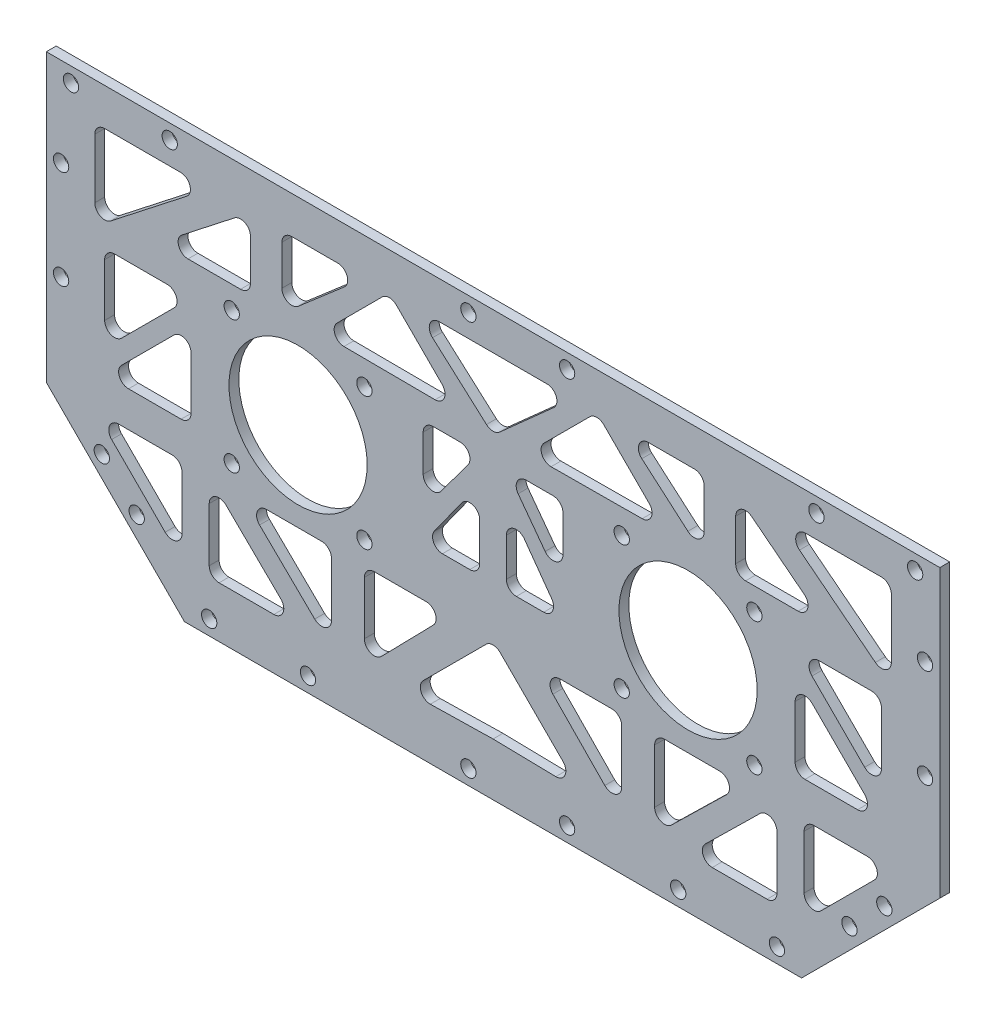
SolidWorks part; units mm, degrees
material "Thornel Mat VMA"
ref_plane "前视基准面" through (0, 0, 0) normal (0, 0, 1) x (1, 0, 0)
ref_plane "上视基准面" through (0, 0, 0) normal (0, 1, 0) x (1, 0, 0)
ref_plane "右视基准面" through (0, 0, 0) normal (1, 0, 0) x (0, 0, -1)
sketch "草图1" plane through (0, 0, 0) normal (0, 0, 1) x (1, 0, 0)
  line L0 (-39.5, 0) -> (39.5, 0) construction
  line L7 (-62.5, -32.4324) -> (70.1149, 36.3839) construction
  line L8 (-92.5, -48) -> (-80.6781, -41.8654) construction
  line L9 (-39.5, 0) -> (-52.935, -13.435) construction
  line L10 (-39.5, 0) -> (-39.5, -19) construction
  line L11 (-52.935, 13.435) -> (-26.065, -13.435) construction
  line L12 (-39.5, 0) -> (-26.065, 13.435) construction
  line L13 (26.065, 13.435) -> (39.5, 0) construction
  line L14 (39.5, 0) -> (52.935, -13.435) construction
  line L15 (39.5, 0) -> (39.5, -24.0416) construction
  line L16 (26.065, -13.435) -> (39.5, 0) construction
  line L17 (39.5, 0) -> (52.935, 13.435) construction
  line L18 (39.5, 0) -> (63.5416, 0) construction
  line L19 (-90.5, 18) -> (-90.5, -18)
  line L20 (-62.5, -46) -> (62.5, -46)
  line L21 (90.5, 18) -> (90.5, -18)
  line L23 (62.2753, 0) -> (62.2753, 18) construction
  line L25 (0, 48) -> (0, -63.7675) construction
  line L27 (-20, -40) -> (20, -40) construction
  line L28 (-20, -40) -> (-20, -46) construction
  line L29 (-20, -46) -> (20, -46) construction
  line L30 (20, -40) -> (20, -46) construction
  line L31 (-20, -40) -> (20, -46) construction
  line L32 (-20, -46) -> (20, -40) construction
  line L36 (-77.2639, -21.4142) -> (-66.4216, -32.2565)
  line L38 (-63.0074, -30.8423) -> (-63.0074, -20)
  line L51 (-62.5, 32.4324) -> (62.5, -32.4324) construction
  line L67 (0, 29.9183) -> (47.4731, 22.681) construction
  line L68 (48.1242, -22.4415) -> (0, -29.8407) construction
  line L93 (90.5, -18) -> (62.5, -46)
  line L94 (-62.5, -46) -> (-90.5, -18)
  line L95 (-90.5, 18) -> (-90.5, 39.9996)
  line L98 (90.5, 39.9996) -> (90.5, 18)
  line L99 (-65.0074, -18) -> (-75.8497, -18)
  line L100 (-57.5, -22.7661) -> (-57.5, -33.6707)
  line L101 (-55.5, -35.6707) -> (-44.3922, -35.6707)
  line L102 (-42.9911, -32.2435) -> (-54.0989, -21.3389)
  line L109 (-45.9021, -18) -> (-34.7336, -18)
  line L110 (-32.7336, -20) -> (-32.7336, -30.9185)
  line L112 (-36.1317, -32.3487) -> (-47.3002, -21.4301)
  line L114 (-26.065, -20) -> (-26.065, -30.764)
  line L115 (-22.6348, -32.1621) -> (-12.1117, -21.3981)
  line L116 (-13.5419, -18) -> (-24.065, -18)
  line L117 (-1.4142, -19.4142) -> (-14.1576, -32.1576)
  line L118 (-12.7034, -35.5714) -> (0, -35.3174)
  line L119 (-80.6781, 30.4324) -> (-80.6781, 18.4111)
  line L120 (-77.4461, 16.8356) -> (-62.0726, 28.8569)
  line L121 (-63.3045, 32.4324) -> (-78.6781, 32.4324)
  line L122 (-52.377, 29.9052) -> (-63.0295, 21.5755)
  line L123 (-61.7975, 18) -> (-51.145, 18)
  line L124 (-49.145, 20) -> (-49.145, 28.3297)
  line L125 (-1.3315, 19.1879) -> (-12.2625, 28.94)
  line L126 (-10.931, 32.4324) -> (10.931, 32.4324)
  line L127 (-42.7754, 30.4324) -> (-42.7754, 22.37)
  line L128 (-39.4682, 20.8564) -> (-30.1332, 28.9188)
  line L129 (-31.4405, 32.4324) -> (-40.7754, 32.4324)
  line L130 (-19.6046, 31.0182) -> (-10.3179, 21.7316)
  line L131 (-11.7442, 18.3174) -> (-30.206, 18.4289)
  line L132 (-31.6082, 21.8431) -> (-22.433, 31.0182)
  line L133 (1.3315, 19.1879) -> (12.2625, 28.94)
  line L134 (12.7034, -35.5714) -> (0, -35.3174)
  line L135 (1.4142, -19.4142) -> (14.1576, -32.1576)
  line L136 (63.0074, -30.8423) -> (63.0074, -20)
  line L137 (77.2639, -21.4142) -> (66.4216, -32.2565)
  line L138 (65.0074, -18) -> (75.8497, -18)
  line L139 (55.5, -35.6707) -> (44.3922, -35.6707)
  line L140 (57.5, -22.7661) -> (57.5, -33.6707)
  line L141 (42.9911, -32.2435) -> (54.0989, -21.3389)
  line L142 (32.7336, -20) -> (32.7336, -30.9185)
  line L143 (45.9021, -18) -> (34.7336, -18)
  line L144 (36.1317, -32.3487) -> (47.3002, -21.4301)
  line L145 (22.6348, -32.1621) -> (12.1117, -21.3981)
  line L146 (26.065, -20) -> (26.065, -30.764)
  line L147 (13.5419, -18) -> (24.065, -18)
  line L148 (77.4461, 16.8356) -> (62.0726, 28.8569)
  line L149 (80.6781, 30.4324) -> (80.6781, 18.4111)
  line L150 (63.3045, 32.4324) -> (78.6781, 32.4324)
  line L151 (61.7975, 18) -> (51.145, 18)
  line L152 (52.377, 29.9052) -> (63.0295, 21.5755)
  line L153 (49.145, 20) -> (49.145, 28.3297)
  line L154 (39.4682, 20.8564) -> (30.1332, 28.9188)
  line L155 (42.7754, 30.4324) -> (42.7754, 22.37)
  line L156 (31.4405, 32.4324) -> (40.7754, 32.4324)
  line L157 (11.7442, 18.3174) -> (30.206, 18.4289)
  line L158 (19.6046, 31.0182) -> (10.3179, 21.7316)
  line L159 (31.6082, 21.8431) -> (22.433, 31.0182)
  line L160 (-12.1576, 13.435) -> (-6.6802, 13.435)
  line L161 (-14.1576, 11.435) -> (-14.1576, 4.0523)
  line L162 (-10.5514, 2.8607) -> (-5.074, 10.2434)
  line L163 (-6.3308, 2.951) -> (-11.8845, -4.7851)
  line L164 (-10.2598, -7.9514) -> (-4.7061, -7.9514)
  line L165 (-2.7061, -5.9514) -> (-2.7061, 1.7846)
  line L175 (10.2598, -7.9514) -> (4.7061, -7.9514)
  line L176 (6.3308, 2.951) -> (11.8845, -4.7851)
  line L177 (2.7061, -5.9514) -> (2.7061, 1.7846)
  line L178 (14.1576, 11.435) -> (14.1576, 4.0523)
  line L179 (10.5514, 2.8607) -> (5.074, 10.2434)
  line L180 (12.1576, 13.435) -> (6.6802, 13.435)
  line L181 (-76.6781, 11.435) -> (-66.0151, 11.435)
  line L182 (-64.6009, 8.0208) -> (-75.2639, -2.6422)
  line L183 (-78.6781, -1.2279) -> (-78.6781, 9.435)
  line L184 (-64.6009, 3.2678) -> (-75.2639, -7.3952)
  line L185 (-73.8497, -10.8094) -> (-63.1867, -10.8094)
  line L186 (-61.1867, -8.8094) -> (-61.1867, 1.8536)
  line L187 (73.8497, -10.8094) -> (63.1867, -10.8094)
  line L188 (64.6009, 3.2678) -> (75.2639, -7.3952)
  line L189 (61.1867, -8.8094) -> (61.1867, 1.8536)
  line L190 (64.6009, 8.0208) -> (75.2639, -2.6422)
  line L191 (76.6781, 11.435) -> (66.0151, 11.435)
  line L192 (78.6781, -1.2279) -> (78.6781, 9.435)
  line L193 (62.5, -46) -> (62.5, -13.435) construction
  line L194 (-90.5, 39.9996) -> (90.5, 39.9996)
  line L195 (90.5, -18) -> (62.5, -18) construction
  line L196 (-90.5, -18) -> (-57.5, -18) construction
  line L197 (-62.5, -46) -> (-62.5, -18) construction
  circle A16 centre (-39.5, 0) radius 19 construction
  circle A30 centre (-52.935, -13.435) radius 1.55
  circle A33 centre (-52.935, 13.435) radius 1.55
  circle A34 centre (-26.065, -13.435) radius 1.55
  circle A35 centre (-26.065, 13.435) radius 1.55
  circle A48 centre (-39.5, 0) radius 14
  circle A49 centre (39.5, 0) radius 14
  circle A50 centre (57.5, -43) radius 1.55
  circle A51 centre (37.5, -43) radius 1.55
  circle A52 centre (-57.5, -43) radius 1.55
  circle A53 centre (-37.5, -43) radius 1.55
  circle A54 centre (-85.5, 37) radius 1.55
  circle A55 centre (-65.5, 37) radius 1.55
  circle A56 centre (65.5, 37) radius 1.55
  circle A57 centre (85.5, 37) radius 1.55
  circle A58 centre (15, -43) radius 1.55
  circle A59 centre (-5, -43) radius 1.55
  circle A60 centre (-5, 37) radius 1.55
  circle A61 centre (15, 37) radius 1.55
  circle A68 centre (-87.5, 21.9996) radius 1.55
  circle A69 centre (-87.5, 1.9996) radius 1.55
  circle A70 centre (87.5, 21.9996) radius 1.55
  circle A71 centre (87.5, 1.9996) radius 1.55
  circle A112 centre (39.5, 0) radius 19 construction
  circle A113 centre (26.065, 13.435) radius 1.55
  circle A114 centre (52.935, 13.435) radius 1.55
  circle A115 centre (52.935, -13.435) radius 1.55
  circle A116 centre (26.065, -13.435) radius 1.55
  arc A117 (-32.7336, -20) -> (-34.7336, -18) centre (-34.7336, -20) ccw
  arc A118 (-13.5419, -18) -> (-12.1117, -21.3981) centre (-13.5419, -20) cw
  arc A119 (-22.6348, -32.1621) -> (-26.065, -30.764) centre (-24.065, -30.764) cw
  arc A120 (-26.065, -20) -> (-24.065, -18) centre (-24.065, -20) cw
  arc A121 (-10.931, 32.4324) -> (-12.2625, 28.94) centre (-10.931, 30.4324) ccw
  arc A122 (-31.6082, 21.8431) -> (-30.206, 18.4289) centre (-30.1939, 20.4289) ccw
  arc A123 (-11.7442, 18.3174) -> (-10.3179, 21.7316) centre (-11.7322, 20.3174) ccw
  arc A124 (-19.6046, 31.0182) -> (-22.433, 31.0182) centre (-21.0188, 29.604) ccw
  arc A125 (-31.4405, 32.4324) -> (-30.1332, 28.9188) centre (-31.4405, 30.4324) cw
  arc A126 (-39.4682, 20.8564) -> (-42.7754, 22.37) centre (-40.7754, 22.37) cw
  arc A127 (-42.7754, 30.4324) -> (-40.7754, 32.4324) centre (-40.7754, 30.4324) cw
  arc A128 (-52.377, 29.9052) -> (-49.145, 28.3297) centre (-51.145, 28.3297) cw
  arc A129 (-49.145, 20) -> (-51.145, 18) centre (-51.145, 20) cw
  arc A130 (-61.7975, 18) -> (-63.0295, 21.5755) centre (-61.7975, 20) cw
  arc A131 (-62.0726, 28.8569) -> (-63.3045, 32.4324) centre (-63.3045, 30.4324) ccw
  arc A132 (-80.6781, 30.4324) -> (-78.6781, 32.4324) centre (-78.6781, 30.4324) cw
  arc A133 (-80.6781, 18.4111) -> (-77.4461, 16.8356) centre (-78.6781, 18.4111) ccw
  arc A134 (-12.7034, -35.5714) -> (-14.1576, -32.1576) centre (-12.7434, -33.5718) cw
  arc A135 (-63.0074, -20) -> (-65.0074, -18) centre (-65.0074, -20) ccw
  arc A136 (-77.2639, -21.4142) -> (-75.8497, -18) centre (-75.8497, -20) cw
  arc A137 (-66.4216, -32.2565) -> (-63.0074, -30.8423) centre (-65.0074, -30.8423) ccw
  arc A138 (-57.5, -33.6707) -> (-55.5, -35.6707) centre (-55.5, -33.6707) ccw
  arc A139 (-44.3922, -35.6707) -> (-42.9911, -32.2435) centre (-44.3922, -33.6707) ccw
  arc A140 (-54.0989, -21.3389) -> (-57.5, -22.7661) centre (-55.5, -22.7661) ccw
  arc A141 (-45.9021, -18) -> (-47.3002, -21.4301) centre (-45.9021, -20) ccw
  arc A142 (-32.7336, -30.9185) -> (-36.1317, -32.3487) centre (-34.7336, -30.9185) cw
  arc A143 (10.931, 32.4324) -> (12.2625, 28.94) centre (10.931, 30.4324) cw
  arc A144 (12.7034, -35.5714) -> (14.1576, -32.1576) centre (12.7434, -33.5718) ccw
  arc A145 (66.4216, -32.2565) -> (63.0074, -30.8423) centre (65.0074, -30.8423) cw
  arc A146 (63.0074, -20) -> (65.0074, -18) centre (65.0074, -20) cw
  arc A147 (77.2639, -21.4142) -> (75.8497, -18) centre (75.8497, -20) ccw
  arc A148 (57.5, -33.6707) -> (55.5, -35.6707) centre (55.5, -33.6707) cw
  arc A149 (44.3922, -35.6707) -> (42.9911, -32.2435) centre (44.3922, -33.6707) cw
  arc A150 (54.0989, -21.3389) -> (57.5, -22.7661) centre (55.5, -22.7661) cw
  arc A151 (32.7336, -20) -> (34.7336, -18) centre (34.7336, -20) cw
  arc A152 (45.9021, -18) -> (47.3002, -21.4301) centre (45.9021, -20) cw
  arc A153 (32.7336, -30.9185) -> (36.1317, -32.3487) centre (34.7336, -30.9185) ccw
  arc A154 (22.6348, -32.1621) -> (26.065, -30.764) centre (24.065, -30.764) ccw
  arc A155 (13.5419, -18) -> (12.1117, -21.3981) centre (13.5419, -20) ccw
  arc A156 (26.065, -20) -> (24.065, -18) centre (24.065, -20) ccw
  arc A157 (80.6781, 18.4111) -> (77.4461, 16.8356) centre (78.6781, 18.4111) cw
  arc A158 (62.0726, 28.8569) -> (63.3045, 32.4324) centre (63.3045, 30.4324) cw
  arc A159 (80.6781, 30.4324) -> (78.6781, 32.4324) centre (78.6781, 30.4324) ccw
  arc A160 (61.7975, 18) -> (63.0295, 21.5755) centre (61.7975, 20) ccw
  arc A161 (52.377, 29.9052) -> (49.145, 28.3297) centre (51.145, 28.3297) ccw
  arc A162 (49.145, 20) -> (51.145, 18) centre (51.145, 20) ccw
  arc A163 (39.4682, 20.8564) -> (42.7754, 22.37) centre (40.7754, 22.37) ccw
  arc A164 (31.4405, 32.4324) -> (30.1332, 28.9188) centre (31.4405, 30.4324) ccw
  arc A165 (42.7754, 30.4324) -> (40.7754, 32.4324) centre (40.7754, 30.4324) ccw
  arc A166 (11.7442, 18.3174) -> (10.3179, 21.7316) centre (11.7322, 20.3174) cw
  arc A167 (31.6082, 21.8431) -> (30.206, 18.4289) centre (30.1939, 20.4289) cw
  arc A168 (19.6046, 31.0182) -> (22.433, 31.0182) centre (21.0188, 29.604) cw
  arc A169 (-1.3315, 19.1879) -> (1.3315, 19.1879) centre (0, 20.6803) ccw
  arc A170 (1.4142, -19.4142) -> (-1.4142, -19.4142) centre (0, -20.8284) ccw
  arc A171 (-2.7061, 1.7846) -> (-6.3308, 2.951) centre (-4.7061, 1.7846) ccw
  arc A172 (-2.7061, -5.9514) -> (-4.7061, -7.9514) centre (-4.7061, -5.9514) cw
  arc A173 (-10.2598, -7.9514) -> (-11.8845, -4.7851) centre (-10.2598, -5.9514) cw
  arc A174 (-6.6802, 13.435) -> (-5.074, 10.2434) centre (-6.6802, 11.435) cw
  arc A181 (-10.5514, 2.8607) -> (-14.1576, 4.0523) centre (-12.1576, 4.0523) cw
  arc A182 (-12.1576, 13.435) -> (-14.1576, 11.435) centre (-12.1576, 11.435) ccw
  arc A186 (10.2598, -7.9514) -> (11.8845, -4.7851) centre (10.2598, -5.9514) ccw
  arc A187 (2.7061, 1.7846) -> (6.3308, 2.951) centre (4.7061, 1.7846) cw
  arc A188 (2.7061, -5.9514) -> (4.7061, -7.9514) centre (4.7061, -5.9514) ccw
  arc A189 (10.5514, 2.8607) -> (14.1576, 4.0523) centre (12.1576, 4.0523) ccw
  arc A190 (6.6802, 13.435) -> (5.074, 10.2434) centre (6.6802, 11.435) ccw
  arc A191 (12.1576, 13.435) -> (14.1576, 11.435) centre (12.1576, 11.435) cw
  arc A192 (-64.6009, 3.2678) -> (-61.1867, 1.8536) centre (-63.1867, 1.8536) cw
  arc A193 (-61.1867, -8.8094) -> (-63.1867, -10.8094) centre (-63.1867, -8.8094) cw
  arc A194 (-73.8497, -10.8094) -> (-75.2639, -7.3952) centre (-73.8497, -8.8094) cw
  arc A195 (-66.0151, 11.435) -> (-64.6009, 8.0208) centre (-66.0151, 9.435) cw
  arc A196 (-75.2639, -2.6422) -> (-78.6781, -1.2279) centre (-76.6781, -1.2279) cw
  arc A197 (-78.6781, 9.435) -> (-76.6781, 11.435) centre (-76.6781, 9.435) cw
  arc A198 (73.8497, -10.8094) -> (75.2639, -7.3952) centre (73.8497, -8.8094) ccw
  arc A199 (64.6009, 3.2678) -> (61.1867, 1.8536) centre (63.1867, 1.8536) ccw
  arc A200 (61.1867, -8.8094) -> (63.1867, -10.8094) centre (63.1867, -8.8094) ccw
  arc A201 (66.0151, 11.435) -> (64.6009, 8.0208) centre (66.0151, 9.435) ccw
  arc A202 (75.2639, -2.6422) -> (78.6781, -1.2279) centre (76.6781, -1.2279) ccw
  arc A203 (78.6781, 9.435) -> (76.6781, 11.435) centre (76.6781, 9.435) ccw
  circle A204 centre (79.2574, -25) radius 1.55
  circle A205 centre (72.1863, -32.0711) radius 1.55
  circle A206 centre (-79.2574, -25) radius 1.55
  circle A207 centre (-72.1863, -32.0711) radius 1.55
  point P0 (0, 0)
  point P9 (0, 0)
  point P51 (-39.5, 0)
  point P77 (0, -43)
  point P123 (-34.9934, 18.4578)
  point P152 (-80.6781, -18)
  point P161 (-57.5, -18)
  point P170 (0, 32.4324)
  point P190 (2, 42)
  point P193 (2, 30.8273)
  point P196 (-2, 31.4371)
  point P201 (2, 28.3995)
  point P206 (-2, 21)
  point P213 (-2, -39)
  point P216 (-2, -31.3623)
  point P221 (2, -28.3191)
  point P224 (2, -21)
  point P263 (0, 18)
  point P266 (0, -18)
  point P351 (0, 0)
  dimension "D4" = 3
  dimension "D5" = 45
  dimension "D6" = 45
  dimension "D8" = 45
  dimension "D12" = 5
  dimension "D20" = 3.1
  dimension "D16" = 3.1
  dimension "D30" = 5
  dimension "D32" = 3
  dimension "D34" = 3
  dimension "D36" = 5
  dimension "D40" = 2
  dimension "D44" = 2
  dimension "D42" = 2
  dimension "D49" = 10
  dimension "D50" = 7
  dimension "D35" = 5
  dimension "D39" = 2
  dimension "D41" = 2
  dimension "D43" = 2
  dimension "D15" = 3.1
  dimension "D24" = 3.1
  dimension "D7" = 45
  dimension "D9" = 45
  dimension "D10" = 45
  dimension "D11" = 45
  dimension "D13" = 3
  dimension "D14" = 20
  dimension "D17" = 20
  dimension "D18" = 20
  dimension "D19" = 3
  dimension "D21" = 20
  dimension "D22" = 3
  dimension "D23" = 20
  dimension "D25" = 10
  dimension "D26" = 5
  dimension "D27" = 20
  dimension "D28" = 40
  dimension "D29" = 6
  dimension "D31" = 20
  dimension "D33" = 3
  dimension "D37" = 5
  dimension "D38" = 3
  dimension "D45" = 5
  dimension "D46" = 7
  dimension "D47" = 3
  dimension "D48" = 3
  dimension "D51" = 18
  dimension "D52" = 18
extrude "凸台-拉伸1" add sketch "草图1" along normal blind 2
